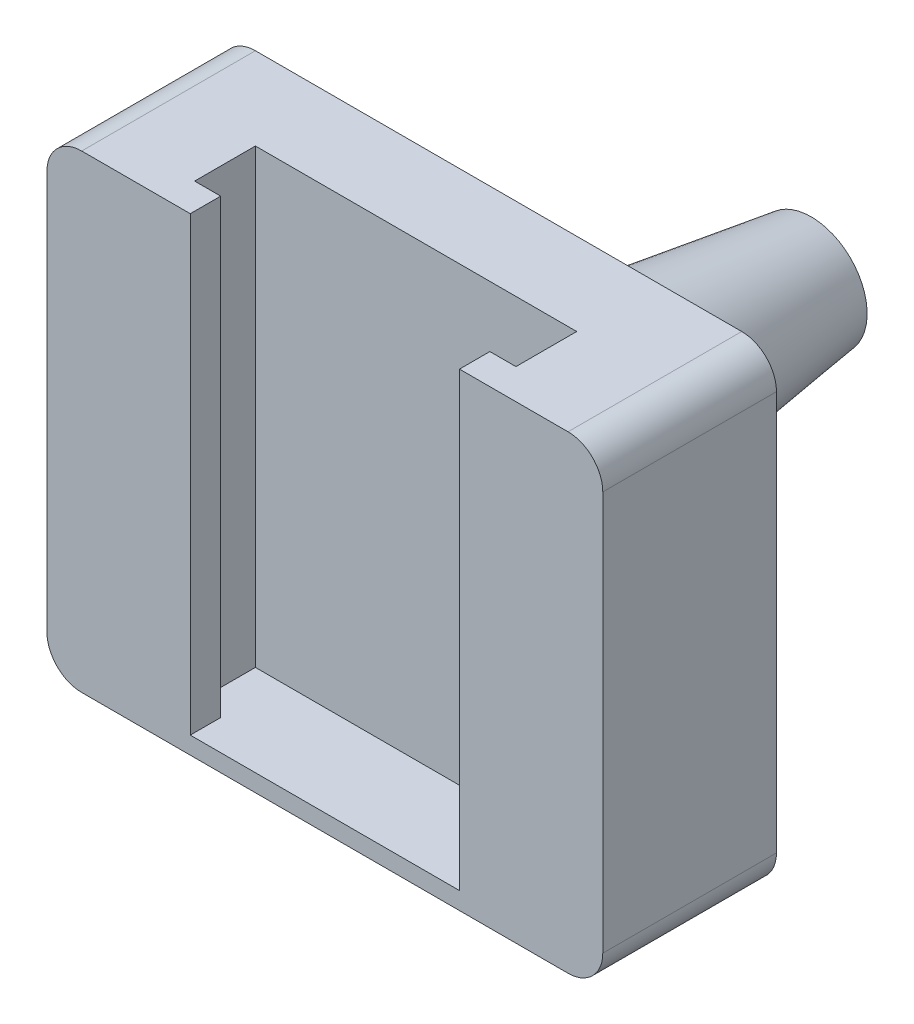
SolidWorks part; units mm, degrees
ref_plane "Front Plane" through (0, 0, 0) normal (0, 0, 1) x (1, 0, 0)
ref_plane "Top Plane" through (0, 0, 0) normal (0, 1, 0) x (1, 0, 0)
ref_plane "Right Plane" through (0, 0, 0) normal (1, 0, 0) x (0, 0, -1)
sketch "Sketch1" plane through (0, 0, 0) normal (0, 0, 1) x (1, 0, 0)
  line L1 (-16, -13.5) -> (16, -13.5)
  line L2 (-16, -13.5) -> (-16, 13.5)
  line L3 (-16, 13.5) -> (16, 13.5)
  line L4 (16, -13.5) -> (16, 13.5)
  line L5 (-16, -13.5) -> (16, 13.5) construction
  line L6 (-16, 13.5) -> (16, -13.5) construction
  point P0 (0, 0)
  dimension "D1" = 32
  dimension "D2" = 27
extrude "Boss-Extrude1" add sketch "Sketch1" along normal blind 10 contours L3 L4 L1 L2
fillet "Fillet1" radius 2 4 edges at (16, 13.5, 5) (-16, 13.5, 5) (16, -13.5, 5) (-16, -13.5, 5)
sketch "Sketch2" plane through (0, 13.5, 0) normal (0, 1, 0) x (1, 0, 0)
  line L0 (-7.75, -10) -> (-7.75, -8.25)
  line L1 (-14, -10) -> (14, -10) construction
  line L2 (-7.75, -8.25) -> (-9.25, -8.25)
  line L3 (-9.25, -8.25) -> (-9.25, -4.75)
  line L4 (-9.25, -4.75) -> (9.25, -4.75)
  line L5 (9.25, -4.75) -> (9.25, -8.25)
  line L6 (9.25, -8.25) -> (7.75, -8.25)
  line L7 (7.75, -8.25) -> (7.75, -10)
  line L8 (0, 0) -> (0, -10) construction
  line L9 (-14, 0) -> (14, 0) construction
  line L10 (-7.75, -10) -> (7.75, -10)
  point P15 (0, -4.75)
  dimension "D1" = 18.5
  dimension "D2" = 1.75
  dimension "D3" = 3.5
  dimension "D4" = 15.5
extrude "Cut-Extrude4" cut sketch "Sketch2" against normal offset from surface (26 mm away) 1 up to face at (0, -13.5, 5)
sketch "Sketch4" plane through (0, 0, 0) normal (0, 0, -1) x (-1, 0, 0)
  line L0 (-15.4142, 12.9142) -> (15.4142, -12.9142) construction
  line L1 (15.4142, -12.9142) -> (-15.4142, -12.9142) construction
  line L2 (-15.4142, -12.9142) -> (15.4142, 12.9142) construction
  arc A0 (-14, 13.5) -> (-16, 11.5) centre (-14, 11.5) ccw construction
  arc A1 (14, -13.5) -> (16, -11.5) centre (14, -11.5) ccw construction
  arc A2 (-16, -11.5) -> (-14, -13.5) centre (-14, -11.5) ccw construction
  arc A3 (16, 11.5) -> (14, 13.5) centre (14, 11.5) ccw construction
  circle A4 centre (0, 0) radius 5.75
  dimension "D1" = 11.5
extrude "Boss-Extrude2" add sketch "Sketch4" along normal blind 18 draft 8
fillet "Fillet2" radius 2 1 edges at (-5.75, 0, 0)
